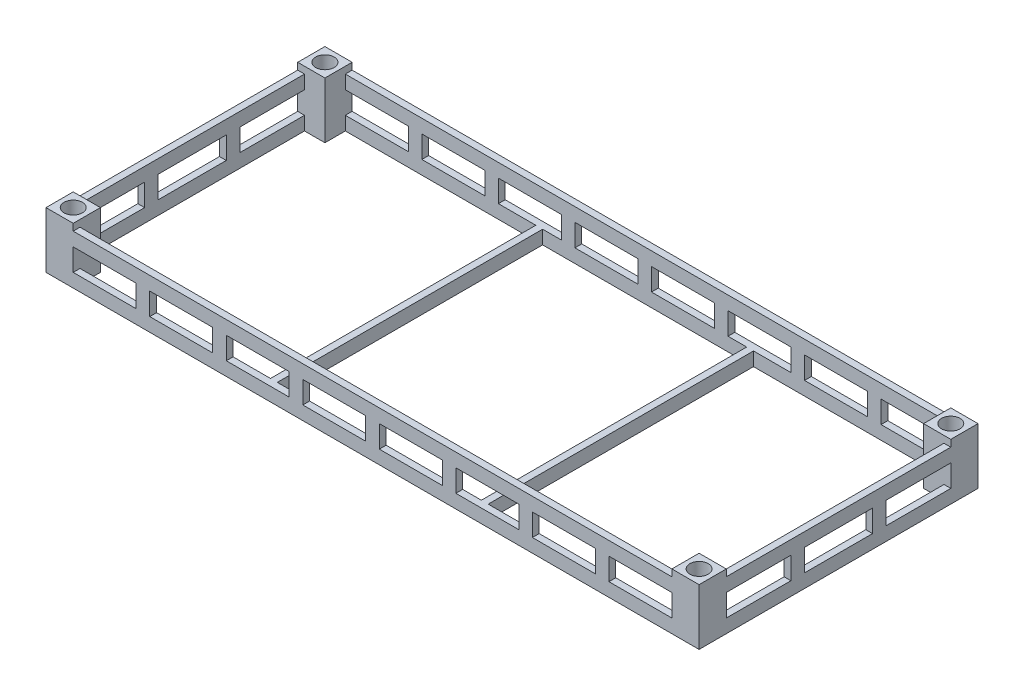
SolidWorks part; units mm, degrees
ref_plane "Front Plane" through (0, 0, 0) normal (0, 0, 1) x (1, 0, 0)
ref_plane "Top Plane" through (0, 0, 0) normal (0, 1, 0) x (1, 0, 0)
ref_plane "Right Plane" through (0, 0, 0) normal (1, 0, 0) x (0, 0, -1)
sketch "Sketch1" plane through (0, 0, 0) normal (0, 1, 0) x (1, 0, 0)
  line L0 (0, 820) -> (60, 820)
  line L1 (0, 0) -> (1920, 0)
  line L2 (0, 0) -> (0, 820)
  line L3 (0, 820) -> (1920, 820)
  line L4 (1920, 0) -> (1920, 820)
  line L5 (60, 820) -> (60, 760)
  line L6 (60, 760) -> (0, 760)
  line L7 (0, 760) -> (0, 765)
  line L8 (0, 765) -> (60, 765)
  line L9 (60, 765) -> (55, 765)
  line L10 (55, 765) -> (55, 820)
  line L11 (55, 820) -> (55, 815)
  line L12 (55, 815) -> (0, 815)
  line L13 (0, 815) -> (5, 815)
  line L14 (5, 815) -> (5, 765)
  line L15 (0, 760) -> (60, 820)
  line L16 (960, 0) -> (960, 820)
  line L17 (960, 820) -> (960, 0)
  line L18 (960, 410) -> (0, 410)
  line L19 (1920, 760) -> (1860, 820)
  line L20 (1915, 815) -> (1915, 765)
  line L21 (1920, 815) -> (1915, 815)
  line L22 (1865, 815) -> (1920, 815)
  line L23 (1865, 820) -> (1865, 815)
  line L24 (1865, 765) -> (1865, 820)
  line L25 (1860, 765) -> (1865, 765)
  line L26 (1920, 765) -> (1860, 765)
  line L27 (1920, 760) -> (1920, 765)
  line L28 (1860, 760) -> (1920, 760)
  line L29 (1860, 820) -> (1860, 760)
  line L30 (1920, 820) -> (1860, 820)
  line L31 (1920, 0) -> (1860, 0)
  line L32 (1860, 0) -> (1860, 60)
  line L33 (1860, 60) -> (1920, 60)
  line L34 (1920, 60) -> (1920, 55)
  line L35 (1920, 55) -> (1860, 55)
  line L36 (1860, 55) -> (1865, 55)
  line L37 (1865, 55) -> (1865, 0)
  line L38 (1865, 0) -> (1865, 5)
  line L39 (1865, 5) -> (1920, 5)
  line L40 (1920, 5) -> (1915, 5)
  line L41 (1915, 5) -> (1915, 55)
  line L42 (1920, 60) -> (1860, 0)
  line L43 (0, 60) -> (60, 0)
  line L44 (5, 5) -> (5, 55)
  line L45 (0, 5) -> (5, 5)
  line L46 (55, 5) -> (0, 5)
  line L47 (55, 0) -> (55, 5)
  line L48 (55, 55) -> (55, 0)
  line L49 (60, 55) -> (55, 55)
  line L50 (0, 55) -> (60, 55)
  line L51 (0, 60) -> (0, 55)
  line L52 (60, 60) -> (0, 60)
  line L53 (60, 0) -> (60, 60)
  line L54 (0, 0) -> (1920, 0)
  line L55 (0, 0) -> (60, 0)
  line L56 (60, 0) -> (60, 20)
  line L57 (60, 20) -> (1860, 20)
  line L58 (1920, 60) -> (1900, 60)
  line L59 (1900, 60) -> (1900, 760)
  line L60 (60, 800) -> (1860, 800)
  line L61 (20, 60) -> (20, 760)
  circle A0 centre (30, 790) radius 25
  circle A1 centre (1890, 790) radius 25
  circle A2 centre (1890, 30) radius 25
  circle A3 centre (30, 30) radius 25
extrude "Boss-Extrude1" add sketch "Sketch1" along normal blind 165 contours L14 L12 L2 L8 | A0 L14 L15 | A0 L15 L8 | L2 L15 L8 | L15 L6 L5 L8 | A0 L8 L10 | L15 L10 L8 L5 | A0 L12 L14 | L12 L10 L0 L2 | A0 L15 L12 | A0 L10 L15 | L10 L15 L3 | L5 L60 L16 L3 | L18 L61 L6 L2 | L52 L61 L18 L2 | L2 L50 L43 | L50 L2 L45 L44 | L49 L53 L52 L43 L50 | L43 A3 L50 | L44 A3 L43 | L50 A3 L48 | L43 L53 L49 L48 | L43 A3 L46 | L48 A3 L43 | L1 L47 L46 L45 L2 | L47 L1 L43 | L46 A3 L44 | L57 L53 L1 L16 | L57 L16 L1 L32 | L42 L37 L35 L32 | A2 L37 L42 | A2 L42 L39 | L37 L42 L1 | L39 L37 L31 L4 | A2 L39 L41 | L41 L39 L4 L35 | L42 L33 L32 L35 | A2 L35 L37 | A2 L42 L35 | L4 L42 L35 | A2 L41 L42 | L59 L33 L4 L28 | L25 L29 L28 L19 L26 | L4 L26 L19 | L20 A1 L19 | L19 A1 L26 | L26 L4 L21 L20 | L3 L23 L22 L21 L4 | L22 A1 L20 | L23 L3 L19 | L19 L29 L25 L24 | L24 A1 L19 | L19 A1 L22 | L26 A1 L24 | L16 L60 L29 L3
sketch "Sketch2" plane through (0, 0, 0) normal (0, 0, 1) x (1, 0, 0)
  line L0 (0, 165) -> (60, 165)
  line L1 (0, 165) -> (1920, 165) construction
  line L2 (60, 165) -> (60, 145)
  line L3 (60, 145) -> (1860, 145)
  line L4 (1860, 145) -> (1860, 165)
  line L5 (1860, 165) -> (60, 165)
  line L6 (1860, 145) -> (1860, 105)
  line L7 (1860, 105) -> (60, 105)
  line L8 (60, 105) -> (60, 145)
  line L9 (60, 105) -> (60, 40)
  line L10 (60, 40) -> (1860, 40)
  line L11 (1860, 105) -> (1860, 40)
  line L12 (960, 105) -> (960, 40)
  line L13 (960, 40) -> (980, 40)
  line L14 (980, 40) -> (980, 105)
  line L15 (980, 105) -> (940, 105)
  line L16 (940, 105) -> (940, 40)
  line L17 (960, 105) -> (1860, 105)
  line L18 (1860, 105) -> (1410, 105)
  line L19 (960, 105) -> (1410, 105)
  line L20 (1185, 105) -> (1185, 40)
  line L21 (1185, 40) -> (1410, 40)
  line L22 (1410, 40) -> (1410, 105)
  line L23 (1635, 105) -> (1635, 40)
  line L24 (960, 105) -> (735, 105)
  line L25 (735, 105) -> (735, 40)
  line L26 (735, 40) -> (510, 40)
  line L27 (510, 40) -> (510, 105)
  line L28 (510, 105) -> (285, 105)
  line L29 (285, 105) -> (285, 40)
  line L30 (755, 40) -> (755, 105)
  line L31 (755, 105) -> (715, 105)
  line L32 (735, 40) -> (755, 40)
  line L33 (715, 105) -> (715, 40)
  line L34 (735, 105) -> (735, 40)
  line L35 (530, 40) -> (530, 105)
  line L36 (530, 105) -> (490, 105)
  line L37 (510, 40) -> (530, 40)
  line L38 (490, 105) -> (490, 40)
  line L39 (510, 105) -> (510, 40)
  line L40 (305, 40) -> (305, 105)
  line L41 (305, 105) -> (265, 105)
  line L42 (285, 40) -> (305, 40)
  line L43 (265, 105) -> (265, 40)
  line L44 (285, 105) -> (285, 40)
  line L45 (1205, 40) -> (1205, 105)
  line L46 (1205, 105) -> (1165, 105)
  line L47 (1185, 40) -> (1205, 40)
  line L48 (1165, 105) -> (1165, 40)
  line L49 (1185, 105) -> (1185, 40)
  line L50 (1430, 40) -> (1430, 105)
  line L51 (1430, 105) -> (1390, 105)
  line L52 (1410, 40) -> (1430, 40)
  line L53 (1390, 105) -> (1390, 40)
  line L54 (1410, 105) -> (1410, 40)
  line L55 (1655, 40) -> (1655, 105)
  line L56 (1655, 105) -> (1615, 105)
  line L57 (1635, 40) -> (1655, 40)
  line L58 (1615, 105) -> (1615, 40)
  line L59 (1635, 105) -> (1635, 40)
  line M7 (1920, 165) -> (0, 165)
extrude "Cut-Extrude1" cut sketch "Sketch2" against normal through all both and the other way through all contours L43 L7 L9 L10 | L40 L10 L38 L28 | L35 L26 L33 L7 | L30 L10 L16 L7 | L48 L17 L14 L10 | L53 L19 L45 L21 | L58 L7 L50 L10 | L55 L10 L11 L7 | L3 L4 L2 M7
sketch "Sketch3" plane through (1920, 0, 0) normal (1, 0, 0) x (0, 0, -1)
  line L0 (820, 165) -> (760, 165)
  line L1 (0, 165) -> (820, 165) construction
  line L2 (760, 165) -> (760, 0)
  line L3 (760, 0) -> (60, 0)
  line L4 (0, 0) -> (820, 0) construction
  line L5 (60, 0) -> (60, 165)
  line L6 (60, 165) -> (760, 165)
  line L7 (60, 165) -> (60, 145)
  line L8 (60, 145) -> (760, 145)
  line L9 (410, 145) -> (310, 145)
  line L10 (310, 145) -> (310, 0)
  line L11 (310, 0) -> (270, 0)
  line L12 (270, 0) -> (270, 145)
  line L13 (410, 145) -> (410, 212.6198)
  line L14 (510, 145) -> (510, 0)
  line L15 (550, 0) -> (550, 145)
  line L16 (760, 145) -> (760, 105)
  line L17 (760, 105) -> (60, 105)
  line L18 (60, 105) -> (60, 40)
  line L19 (60, 40) -> (760, 40)
  line M9 (820, 165) -> (0, 165)
extrude "Cut-Extrude2" cut sketch "Sketch3" against normal through all both and the other way through all contours L8 L13 L6 L5 | L13 L8 L2 M9 | L10 L19 L14 L17 | L15 L19 L2 L17 | L5 L19 L12 L17
sketch "Sketch5" plane through (0, 0, 0) normal (0, -1, 0) x (1, 0, 0)
  line L0 (960, 0) -> (1260, 0)
  line L1 (0, 0) -> (1920, 0) construction
  line L2 (1260, 0) -> (1260, -820)
  line L3 (0, -820) -> (1920, -820) construction
  line L4 (1260, -820) -> (1280, -820)
  line L5 (1280, -820) -> (1280, 0)
  line L6 (1280, 0) -> (1260, 0)
  line L7 (960, 0) -> (660, 0)
  line L8 (660, 0) -> (660, -820)
  line L9 (660, -820) -> (640, -820)
  line L10 (640, -820) -> (640, 0)
  line L11 (640, 0) -> (660, 0)
  line M11 (1860, -800) -> (60, -800)
  line M17 (60, -20) -> (1860, -20)
extrude "Boss-Extrude3" add sketch "Sketch5" against normal blind 40 contours L10 L8 M11 M17 | L5 L2 M11 M17
scale "Scale2" scale about centroid uniform scaling yes scale factor 0.1
sketch "Sketch6" plane through (0, 77.378, 0) normal (0, 1, 0) x (1, 0, 0)
  line L1 (1056, 369) -> (1049, 369)
  line L2 (1056, 369) -> (1056, 376)
  line L3 (1056, 376) -> (1049, 376)
  line L4 (1049, 369) -> (1049, 376)
  line L5 (864, 369) -> (871, 369)
  line L6 (864, 369) -> (864, 376)
  line L7 (864, 376) -> (871, 376)
  line L8 (871, 369) -> (871, 376)
  line L9 (1056, 451) -> (1049, 451)
  line L10 (1056, 451) -> (1056, 444)
  line L11 (1056, 444) -> (1049, 444)
  line L12 (1049, 451) -> (1049, 444)
  line L13 (864, 451) -> (871, 451)
  line L14 (864, 451) -> (864, 444)
  line L15 (864, 444) -> (871, 444)
  line L16 (871, 451) -> (871, 444)
extrude "Boss-Extrude4" add sketch "Sketch6" against normal up to surface (16.5 mm away) up to face at (960, 60.878, -410)
sketch "Sketch7" plane through (0, 77.378, 0) normal (0, 1, 0) x (1, 0, 0)
  line L0 (1052.5, 369) -> (1052.5, 376)
  line L1 (1049, 369) -> (1056, 369) construction
  line L2 (1056, 376) -> (1049, 376) construction
  line L3 (1056, 369) -> (864, 369)
  line L4 (864, 369) -> (864.0294, 369.2165)
  line L5 (864, 451) -> (864, 369)
  line L6 (960, 369) -> (960, 410)
  line L7 (960, 410) -> (864, 410)
  line L8 (864, 451) -> (864.0294, 450.7835)
  line L9 (1056, 451) -> (864, 451)
  line L10 (1052.5, 451) -> (1052.5, 444)
  circle A0 centre (1052.5, 372.5) radius 2.75
  circle A1 centre (867.5, 372.5) radius 2.75
  circle A2 centre (867.5, 447.5) radius 2.75
  circle A3 centre (1052.5, 447.5) radius 2.75
extrude "Cut-Extrude3" cut sketch "Sketch7" against normal through all both and the other way through all contours L0 A0 | L0 A0 | A3 L10 | A3 L10 | A2 | A1
sketch "Sketch8" plane through (0, 60.878, 0) normal (0, -1, 0) x (-1, 0, 0)
  line L1 (-864, 369) -> (-872, 369)
  line L2 (-864, 369) -> (-864, 377)
  line L3 (-864, 377) -> (-872, 377)
  line L4 (-872, 369) -> (-872, 377)
  line L5 (-1056, 451) -> (-1048, 451)
  line L6 (-1056, 451) -> (-1056, 443)
  line L7 (-1056, 443) -> (-1048, 443)
  line L8 (-1048, 451) -> (-1048, 443)
  line L9 (-1056, 369) -> (-1048, 369)
  line L10 (-1056, 369) -> (-1056, 377)
  line L11 (-1056, 377) -> (-1048, 377)
  line L12 (-1048, 369) -> (-1048, 377)
  line L13 (-864, 451) -> (-872, 451)
  line L14 (-864, 451) -> (-864, 443)
  line L15 (-864, 443) -> (-872, 443)
  line L16 (-872, 451) -> (-872, 443)
extrude "Boss-Extrude5" add sketch "Sketch8" against normal blind 16.5
sketch "Sketch9" plane through (0, 60.878, 0) normal (0, -1, 0) x (-1, 0, 0)
  line L0 (-1048, 443) -> (-1056, 451)
  line L1 (-1056, 451) -> (-960, 451)
  line L2 (-864, 451) -> (-1056, 451) construction
  line L3 (-960, 451) -> (-960, 369)
  line L4 (-864, 369) -> (-1056, 369) construction
  line L5 (-960, 369) -> (-960, 410)
  line L6 (-960, 410) -> (-973.0297, 410)
  line L7 (-1056, 369) -> (-960, 369)
  line L8 (-1048, 377) -> (-1056, 369)
  circle A0 centre (-1052, 447) radius 2.7
  circle A1 centre (-868, 447) radius 2.7
  circle A2 centre (-868, 373) radius 2.7
  circle A3 centre (-1052, 373) radius 2.7
extrude "Cut-Extrude4" cut sketch "Sketch9" against normal blind 16.5 contours L0 A0 | L0 A0 | A3 L8 | A3 L8 | A1 | A2
